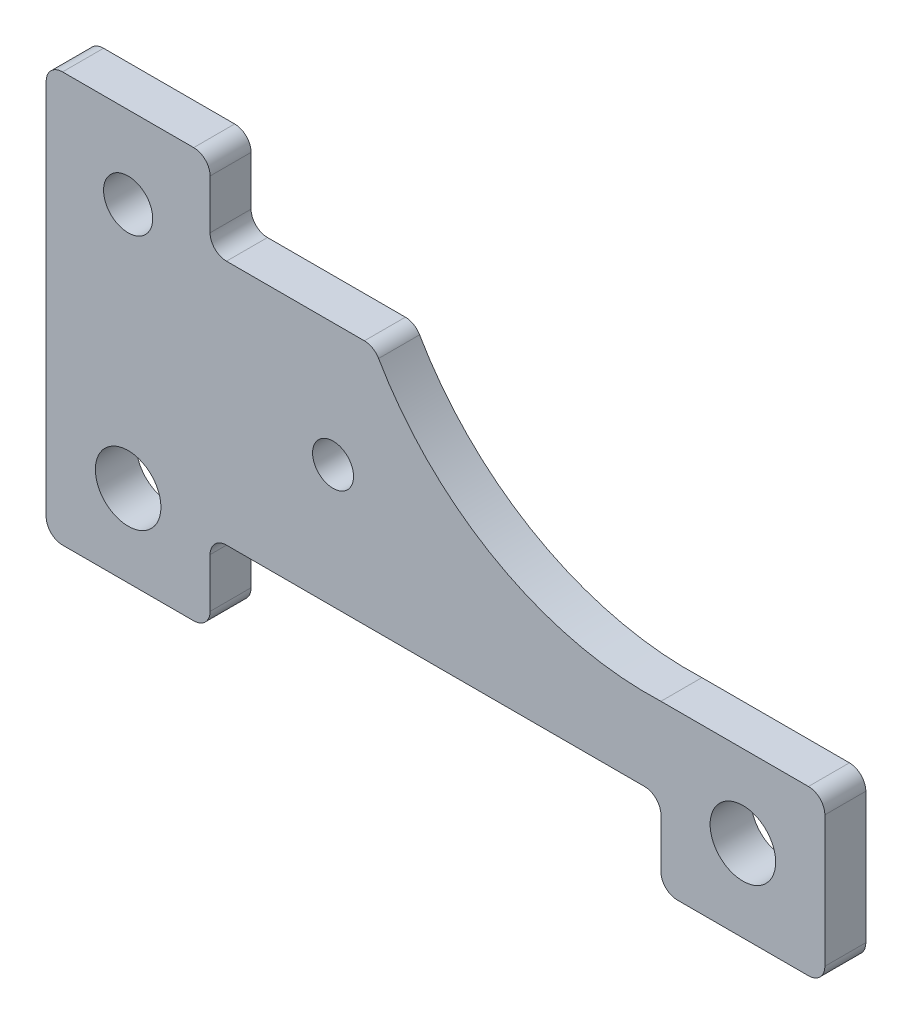
SolidWorks part; units mm, degrees
ref_plane "Front Plane" through (0, 0, 0) normal (0, 0, 1) x (1, 0, 0)
ref_plane "Top Plane" through (0, 0, 0) normal (0, 1, 0) x (1, 0, 0)
ref_plane "Right Plane" through (0, 0, 0) normal (1, 0, 0) x (0, 0, -1)
sketch "Sketch1" plane through (0, 0, 0) normal (0, 0, 1) x (1, 0, 0)
  line L0 (200, 480) -> (200, 420)
  line L1 (20, 0) -> (180, 0)
  line L2 (0, 20) -> (0, 480)
  line L3 (20, 500) -> (180, 500)
  line L4 (950, 20) -> (950, 180)
  line L5 (220, 400) -> (388.2419, 400)
  line L6 (770, 0) -> (930, 0)
  line L7 (750, 200) -> (930, 200)
  line L8 (750, 20) -> (750, 80)
  line L9 (730, 100) -> (220, 100)
  line L10 (200, 80) -> (200, 20)
  arc A0 (0, 480) -> (20, 500) centre (20, 480) cw
  arc A1 (930, 0) -> (950, 20) centre (930, 20) ccw
  arc A2 (20, 0) -> (0, 20) centre (20, 20) cw
  arc A4 (405.5711, 389.9848) -> (750, 200) centre (734.8268, 579.697) ccw
  arc A5 (200, 20) -> (180, 0) centre (180, 20) cw
  arc A6 (220, 100) -> (200, 80) centre (220, 80) ccw
  arc A7 (750, 80) -> (730, 100) centre (730, 80) ccw
  arc A8 (750, 20) -> (770, 0) centre (770, 20) ccw
  arc A9 (930, 200) -> (950, 180) centre (930, 180) cw
  arc A10 (388.2419, 400) -> (405.5711, 389.9848) centre (388.2419, 380) cw
  arc A11 (200, 420) -> (220, 400) centre (220, 420) ccw
  arc A12 (200, 480) -> (180, 500) centre (180, 480) ccw
  circle A13 centre (100, 400) radius 30
  circle A14 centre (100, 100) radius 40
  circle A15 centre (350, 250) radius 25
  circle A16 centre (850, 100) radius 40
  point P7 (0, 500)
  point P13 (0, 0)
  point P25 (200, 0)
  point P28 (200, 100)
  point P31 (750, 100)
  point P34 (750, 0)
  point P37 (950, 200)
  point P40 (400, 400)
  point P54 (111.5564, 427.6848)
  dimension "D3" = 20
  dimension "D4" = 200
  dimension "D12" = 550
  dimension "D13" = 100
  dimension "D2" = 380
  dimension "D14" = 20
  dimension "D15" = 20
  dimension "D16" = 80
  dimension "D17" = 80
  dimension "D18" = 50
  dimension "D19" = 60
  dimension "D5" = 400
  dimension "D6" = 200
  dimension "D7" = 500
  dimension "D8" = 200
  dimension "D9" = 200
  dimension "D10" = 100
  dimension "D11" = 200
  dimension "D20" = 750
  dimension "D21" = 100
  dimension "D22" = 100
  dimension "D23" = 100
  dimension "D24" = 300
  dimension "D25" = 100
  dimension "D26" = 150
  dimension "D27" = 250
extrude "Boss-Extrude1" add sketch "Sketch1" along normal mid plane 50
